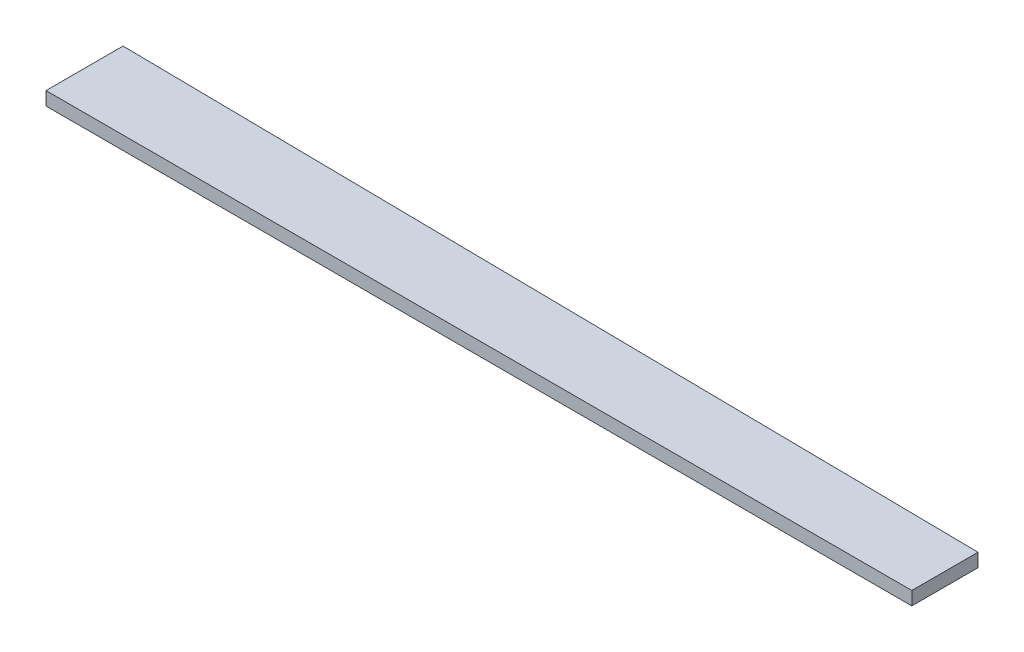
SolidWorks part; units mm, degrees
ref_plane "Plan de face" through (0, 0, 0) normal (0, 0, 1) x (1, 0, 0)
ref_plane "Plan de dessus" through (0, 0, 0) normal (0, 1, 0) x (1, 0, 0)
ref_plane "Plan de droite" through (0, 0, 0) normal (1, 0, 0) x (0, 0, -1)
sketch "Esquisse1" plane through (0, 0, 0) normal (0, 1, 0) x (1, 0, 0)
  line L0 (0, 11.4881) -> (0, 0)
  line L1 (0, 0) -> (129.0879, 0)
  line L2 (129.0879, 0) -> (129.0879, 9.8653)
  line L3 (129.0879, 9.8653) -> (0, 11.4881)
  point P4 (0, 0)
extrude "Boss.-Extru.1" add sketch "Esquisse1" along normal blind 2
